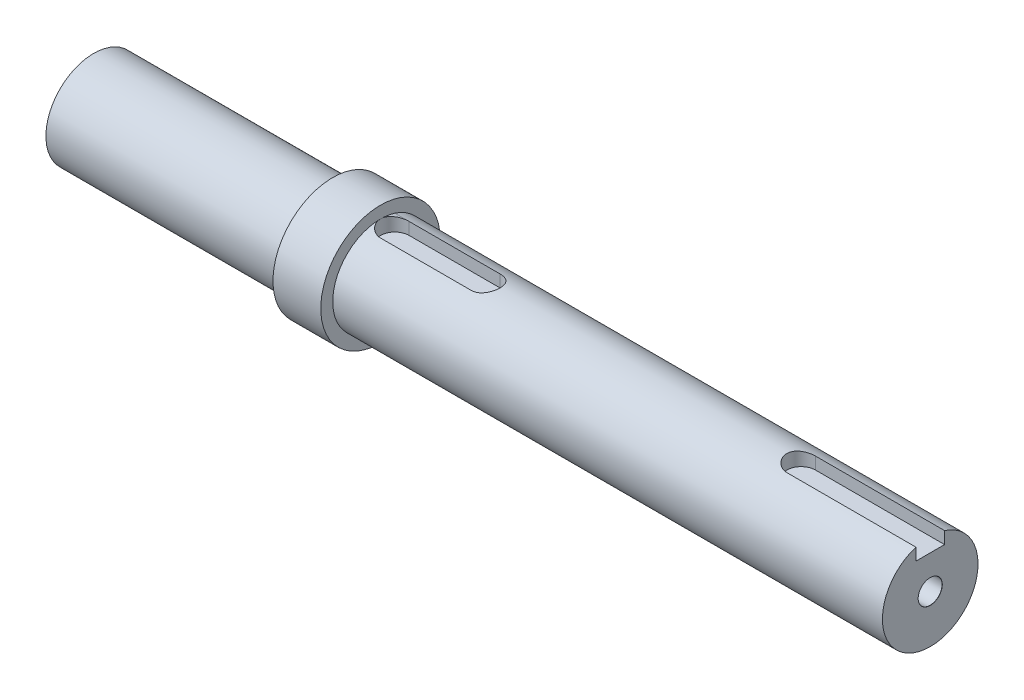
SolidWorks part; units mm, degrees
ref_plane "Front Plane" through (0, 0, 0) normal (0, 0, 1) x (1, 0, 0)
ref_plane "Top Plane" through (0, 0, 0) normal (0, 1, 0) x (1, 0, 0)
ref_plane "Right Plane" through (0, 0, 0) normal (1, 0, 0) x (0, 0, -1)
sketch "Sketch1" plane through (0, 0, 0) normal (0, 1, 0) x (1, 0, 0)
  line L0 (0, 0) -> (0, 10)
  line L1 (0, 10) -> (50, 10)
  line L2 (50, 10) -> (50, 12.5)
  line L3 (50, 12.5) -> (60, 12.5)
  line L4 (60, 12.5) -> (60, 10)
  line L5 (60, 10) -> (175, 10)
  line L6 (175, 10) -> (175, 0)
  line L7 (175, 0) -> (0, 0)
  dimension "D1" = 10
  dimension "D2" = 12.5
  dimension "D3" = 50
  dimension "D4" = 115
  dimension "D5" = 10
  dimension "D6" = 10
revolve "Revolve1" add sketch "Sketch1" angle 360 about L7
hole_wizard "Ø5.0mm Dowel Hole1" positions "3DSketch2" profile "Sketch3" hole size "Ø5.0" standard "ISO"
sketch3d "3DSketch2"
  line L0 (0, 0, 0) -> (0, 0, 14.1375) construction
  line L1 (0, 0, 14.1375) -> (0, 4.6927, 14.1375) construction
  line L3 (0, 0, 0) -> (0, 6.6157, 0) construction
  point P0 (0, 0, 0)
  point P3 (0, 0, 0)
  dimension "D1" = 0
sketch "Sketch3" plane through (0, 0, 0) normal (0, 1, 0) x (0, 0, 1)
  line L0 (0, 0) -> (0, 11.5022)
  line L1 (0, 11.5022) -> (2.5, 10)
  line L2 (2.5, 10) -> (2.5, 0.025)
  line L3 (2.5, 0.025) -> (2.525, 0)
  line L5 (2.525, 0) -> (0, 0)
  line L6 (-2.5, 0.025) -> (-2.525, 0) construction
  line L10 (0, 11.5022) -> (-2.5, 10) construction
  line L11 (0, -6.35) -> (0, 107.95) construction
  dimension "Hole Dia." = 5
  dimension "Hole Depth" = 10
  dimension "Near C'Sink Dia." = 5.05
  dimension "Near C'Sink Angle" = 90
  dimension "Drill Angle" = 118
sketch "Sketch8" plane through (175, 0, 0) normal (1, 0, 0) x (0, 0, -1)
  line L0 (0, 0) -> (15.7935, 0) construction
  line L1 (0, 0) -> (0, 11.1042) construction
hole_wizard "Ø5.0mm Dowel Hole2" positions "3DSketch5" profile "Sketch9" hole size "Ø5.0" standard "ISO"
sketch3d "3DSketch5"
  point P0 (0, 0, 0)
  point P3 (175, 0, 0)
  dimension "D1" = 0
sketch "Sketch9" plane through (175, 0, 0) normal (0, 1, 0) x (0, 0, -1)
  line L0 (0, 0) -> (0, 11.5022)
  line L1 (0, 11.5022) -> (2.5, 10)
  line L2 (2.5, 10) -> (2.5, 0.025)
  line L3 (2.5, 0.025) -> (2.525, 0)
  line L5 (2.525, 0) -> (0, 0)
  line L6 (-2.5, 0.025) -> (-2.525, 0) construction
  line L10 (0, 11.5022) -> (-2.5, 10) construction
  line L11 (0, -6.35) -> (0, 107.95) construction
  dimension "Hole Dia." = 5
  dimension "Hole Depth" = 10
  dimension "Near C'Sink Dia." = 5.05
  dimension "Near C'Sink Angle" = 90
  dimension "Drill Angle" = 118
ref_plane "Plane1" through (0, 10, 0) normal (0, 1, 0) x (1, 0, 0)
sketch "Sketch10" plane through (0, 10, 0) normal (0, 1, 0) x (1, 0, 0)
  line L0 (63, 0) -> (82, 0) construction
  line L1 (63, 3) -> (82, 3)
  line L2 (63, -3) -> (82, -3)
  line L3 (60, -12.5) -> (60, 12.5) construction
  line L4 (175, 0) -> (148, 0) construction
  line L5 (175, 0) -> (175, 15.7935) construction
  line L6 (175, -3) -> (148, -3)
  line L7 (175, 3) -> (148, 3)
  arc A0 (63, 3) -> (63, -3) centre (63, 0) ccw
  arc A1 (82, -3) -> (82, 3) centre (82, 0) ccw
  arc A2 (175, -3) -> (175, 3) centre (175, 0) ccw
  arc A3 (148, 3) -> (148, -3) centre (148, 0) ccw
  point P3 (72.5, 0)
  point P8 (85, 0)
  point P9 (60, 0)
  point P16 (161.5, 0)
  point P21 (0, 0)
  point P22 (145, 0)
  dimension "D2" = 25
  dimension "D1" = 6
  dimension "D3" = 0
  dimension "D4" = 6
  dimension "D5" = 30
extrude "Cut-Extrude1" cut sketch "Sketch10" against normal blind 3
